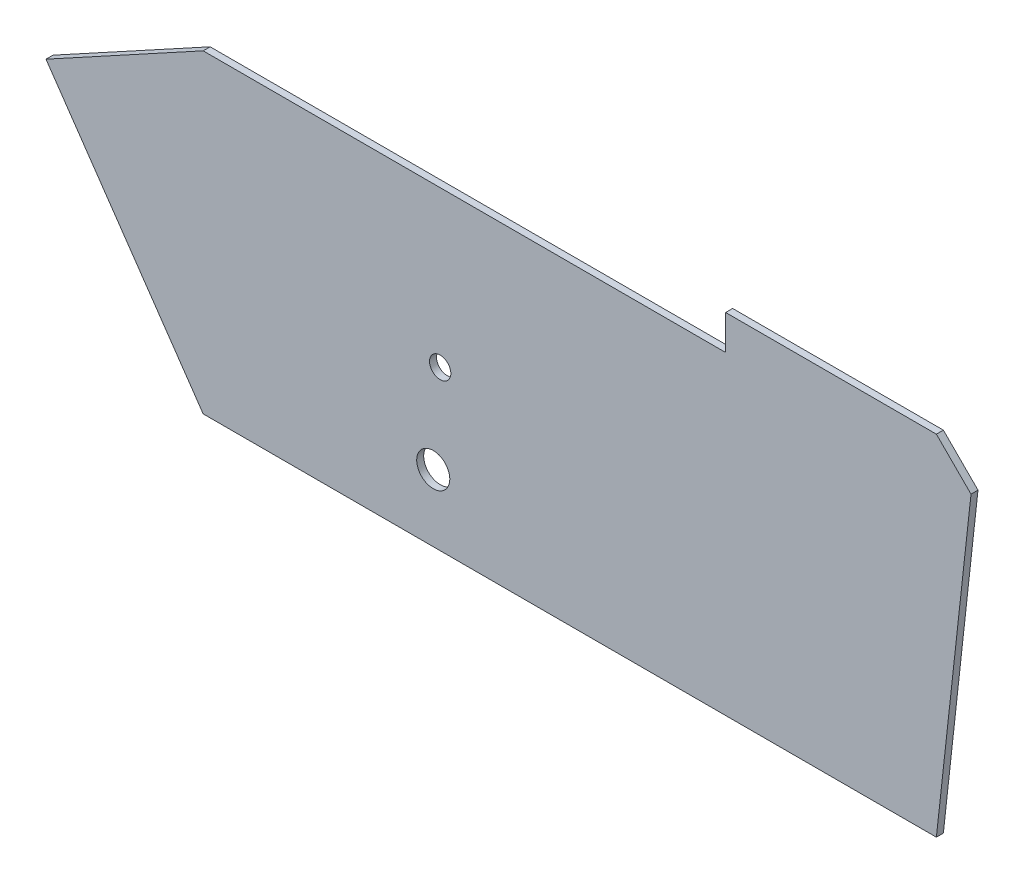
SolidWorks part; units mm, degrees
ref_plane "Front Plane" through (0, 0, 0) normal (0, 0, 1) x (1, 0, 0)
ref_plane "Top Plane" through (0, 0, 0) normal (0, 1, 0) x (1, 0, 0)
ref_plane "Right Plane" through (0, 0, 0) normal (1, 0, 0) x (0, 0, -1)
sketch "Sketch1" plane through (0, 0, 0) normal (0, 0, 1) x (1, 0, 0)
  line L0 (192.0393, 88.9838) -> (201.963, 79.0601)
  line L5 (201.963, 79.0601) -> (192.0393, -11.0162)
  line L6 (192.0393, -11.0162) -> (-18.008, -11.0162)
  line L8 (-18.008, 79.0601) -> (131.6712, 79.0601)
  line L9 (131.6712, 79.0601) -> (131.6712, 88.9838)
  line L10 (131.6712, 88.9838) -> (192.0393, 88.9838)
  line L11 (-18.008, 79.0601) -> (-63.037, 54.4726)
  line L12 (-63.037, 54.4726) -> (-18.008, -11.0162)
extrude "Boss-Extrude1" add sketch "Sketch1" along normal blind 2
sketch "Sketch2" plane through (0, 0, 2) normal (0, 0, 1) x (1, 0, 0)
  circle A0 centre (49.8867, 34.4676) radius 3.05
  circle A1 centre (47.9037, 8.1196) radius 4.7404
extrude "Cut-Extrude1" cut sketch "Sketch2" against normal blind 10
